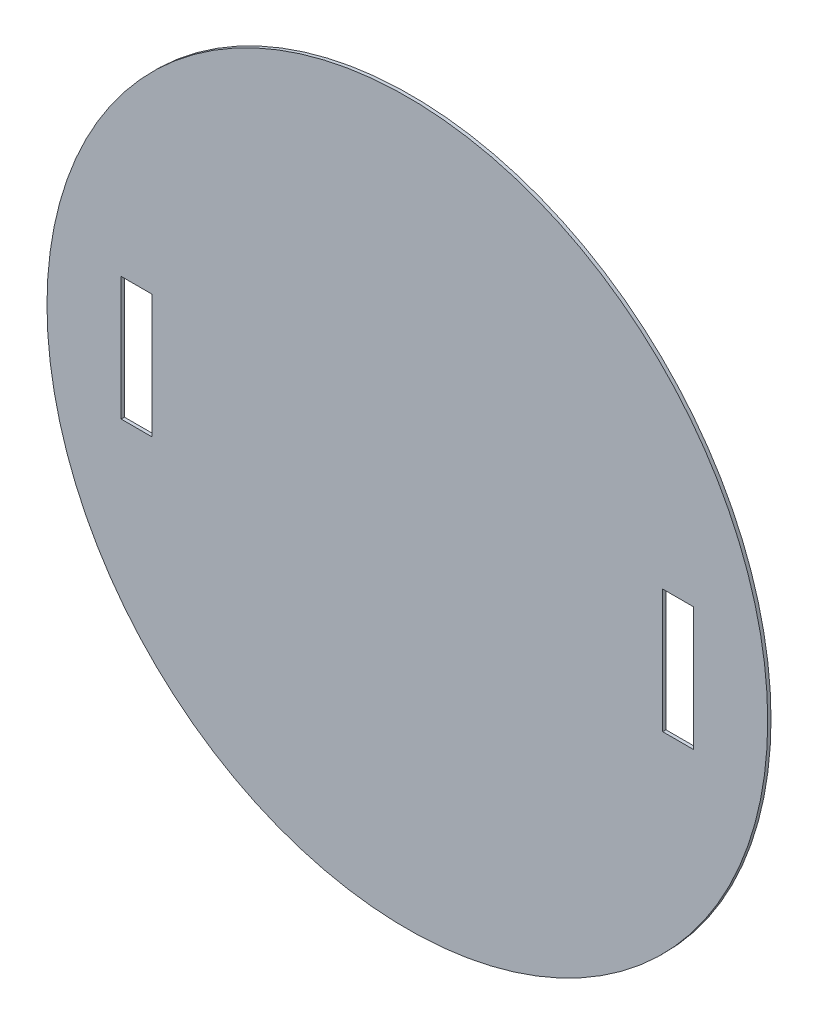
SolidWorks part; units mm, degrees
ref_plane "Front Plane" through (0, 0, 0) normal (0, 0, 1) x (1, 0, 0)
ref_plane "Top Plane" through (0, 0, 0) normal (0, 1, 0) x (1, 0, 0)
ref_plane "Right Plane" through (0, 0, 0) normal (1, 0, 0) x (0, 0, -1)
sketch "Sketch1" plane through (0, 0, 0) normal (0, 0, 1) x (1, 0, 0)
  circle A0 centre (0, 0) radius 175
  dimension "D1" = 350
extrude "Boss-Extrude1" add sketch "Sketch1" along normal blind 1.6
sketch "Sketch2" plane through (0, 0, 1.6) normal (0, 0, 1) x (1, 0, 0)
  line L0 (0, 0) -> (0, 138.2673) construction
  line L1 (-139, 30) -> (-124, 30)
  line L2 (-139, 30) -> (-139, -30)
  line L3 (-139, -30) -> (-124, -30)
  line L4 (-124, 30) -> (-124, -30)
  line L5 (139, -30) -> (124, -30)
  line L6 (124, 30) -> (124, -30)
  line L7 (139, 30) -> (124, 30)
  line L8 (139, 30) -> (139, -30)
  point P7 (-124, 0)
  point P8 (-131.5, 30)
  dimension "D1" = 15
  dimension "D2" = 60
  dimension "D3" = 131.5
extrude "Cut-Extrude1" cut sketch "Sketch2" against normal through all
